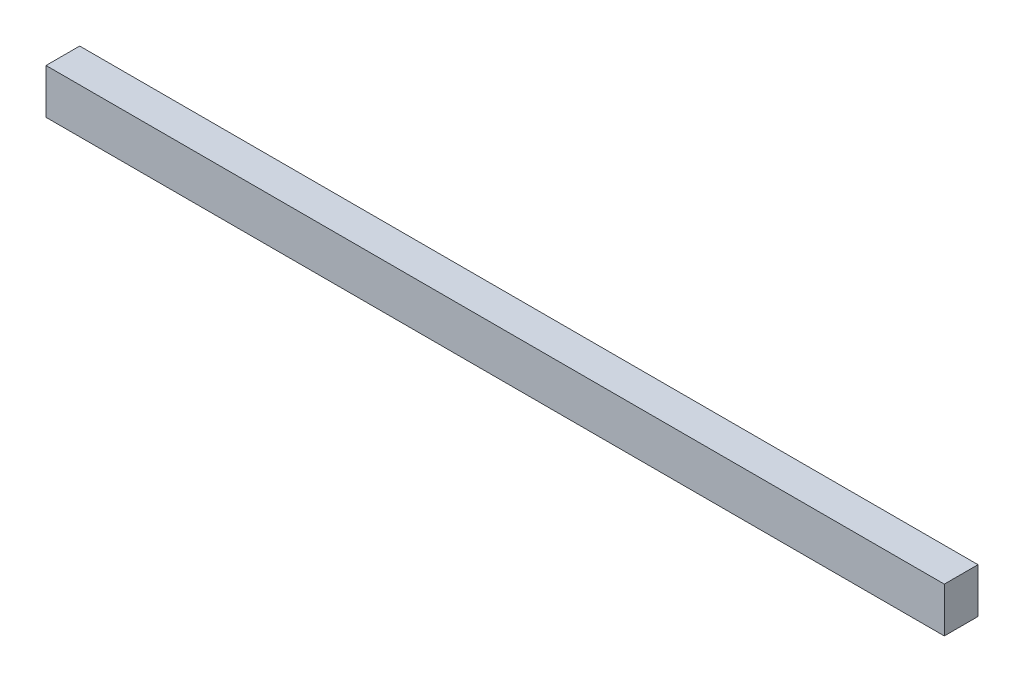
SolidWorks part; units mm, degrees
ref_plane "Front Plane" through (0, 0, 0) normal (0, 0, 1) x (1, 0, 0)
ref_plane "Top Plane" through (0, 0, 0) normal (0, 1, 0) x (1, 0, 0)
ref_plane "Right Plane" through (0, 0, 0) normal (1, 0, 0) x (0, 0, -1)
sketch "Sketch1" plane through (0, 0, 0) normal (0, 0, 1) x (1, 0, 0)
  line L1 (0, 0) -> (508, 0)
  line L2 (0, 0) -> (0, 25.4)
  line L3 (0, 25.4) -> (508, 25.4)
  line L4 (508, 0) -> (508, 25.4)
  dimension "D1" = 25.4
  dimension "D2" = 508
extrude "Boss-Extrude1" add sketch "Sketch1" against normal blind 19.05
